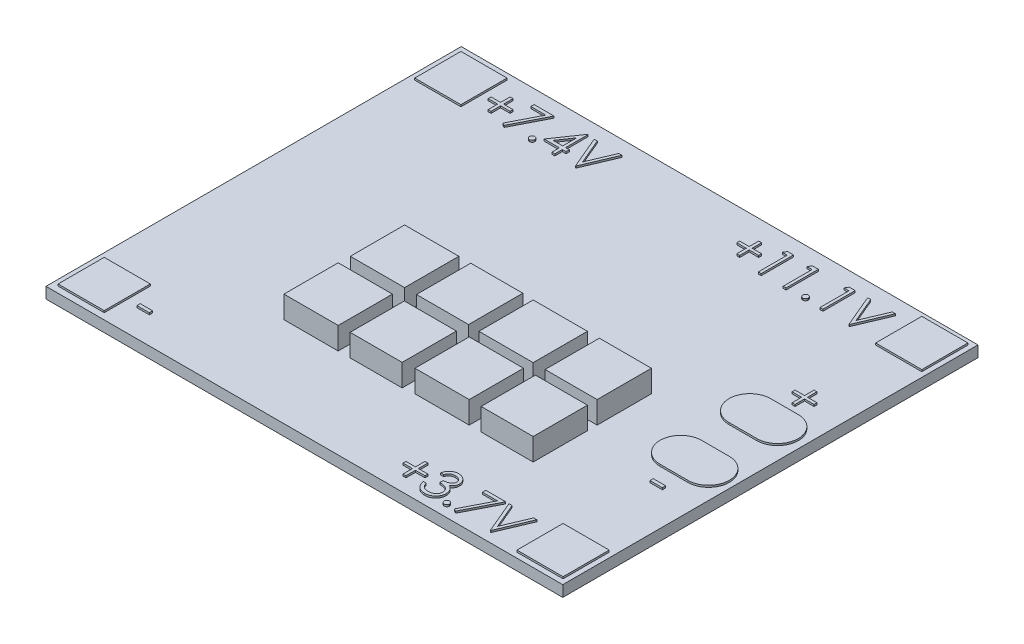
SolidWorks part; units mm, degrees
ref_plane "Front Plane" through (0, 0, 0) normal (0, 0, 1) x (1, 0, 0)
ref_plane "Top Plane" through (0, 0, 0) normal (0, 1, 0) x (1, 0, 0)
ref_plane "Right Plane" through (0, 0, 0) normal (1, 0, 0) x (0, 0, -1)
sketch "Sketch1" plane through (0, 0, 0) normal (0, 1, 0) x (1, 0, 0)
  line L1 (-32.877, 23.7821) -> (23.123, 23.7821)
  line L2 (-32.877, 23.7821) -> (-32.877, -21.2179)
  line L3 (-32.877, -21.2179) -> (23.123, -21.2179)
  line L4 (23.123, 23.7821) -> (23.123, -21.2179)
  dimension "D1" = 45
  dimension "D2" = 56
extrude "Boss-Extrude1" add sketch "Sketch1" along normal blind 1.2
sketch "Sketch2" plane through (0, 1.2, 0) normal (0, 1, 0) x (1, 0, 0)
  line L0 (17.5946, 23.2193) -> (22.5946, 23.2193)
  line L1 (-32.2431, 23.1087) -> (-27.2431, 23.1087)
  line L2 (-32.2431, 23.1087) -> (-32.2431, 18.1087)
  line L3 (-32.2431, 18.1087) -> (-27.2431, 18.1087)
  line L4 (-27.2431, 23.1087) -> (-27.2431, 18.1087)
  line L5 (17.5946, 23.2193) -> (17.5946, 18.2193)
  line L6 (17.5946, 18.2193) -> (22.5946, 18.2193)
  line L7 (22.5946, 23.2193) -> (22.5946, 18.2193)
  line L9 (-43.8468, 1.2821) -> (26.6265, 1.2821)
  line L10 (23.123, 23.7821) -> (-32.877, 23.7821) construction
  line L12 (22.5946, -20.655) -> (22.5946, -15.655)
  line L13 (17.5946, -15.655) -> (22.5946, -15.655)
  line L14 (17.5946, -20.655) -> (17.5946, -15.655)
  line L15 (-27.2431, -20.5444) -> (-27.2431, -15.5444)
  line L16 (-32.2431, -15.5444) -> (-27.2431, -15.5444)
  line L17 (-32.2431, -20.5444) -> (-32.2431, -15.5444)
  line L18 (-32.2431, -20.5444) -> (-27.2431, -20.5444)
  line L19 (17.5946, -20.655) -> (22.5946, -20.655)
  dimension "D1" = 5
  dimension "D2" = 5
  dimension "D3" = 5
  dimension "D4" = 5
  dimension "D5" = 22.5
extrude "Boss-Extrude2" add sketch "Sketch2" along normal blind 0.2 contours L4 L1 L2 L3 | L7 L0 L5 L6 | L14 L19 L12 L13 | L17 L18 L15 L16
sketch "Sketch3" plane through (0, 1.2, 0) normal (0, 1, 0) x (1, 0, 0)
  line L0 (17.1174, 5.0572) -> (20.1292, 5.0572) construction
  line L1 (17.1174, 7.3041) -> (20.1292, 7.3041)
  line L2 (17.1174, 2.8104) -> (20.1292, 2.8104)
  line L3 (17.2974, -2.5988) -> (20.3092, -2.5988) construction
  line L4 (17.2974, -0.3519) -> (20.3092, -0.3519)
  line L5 (17.2974, -4.8456) -> (20.3092, -4.8456)
  line L6 (-40.5161, 1.2821) -> (33.7738, 1.2821)
  line L7 (-32.877, -21.2179) -> (23.123, -21.2179) construction
  arc A0 (17.1174, 7.3041) -> (17.1174, 2.8104) centre (17.1174, 5.0572) ccw
  arc A1 (20.1292, 2.8104) -> (20.1292, 7.3041) centre (20.1292, 5.0572) ccw
  arc A2 (17.2974, -0.3519) -> (17.2974, -4.8456) centre (17.2974, -2.5988) ccw
  arc A3 (20.3092, -4.8456) -> (20.3092, -0.3519) centre (20.3092, -2.5988) ccw
  point P2 (18.6233, 5.0572)
  point P9 (18.8033, -2.5988)
  point P18 (0, 0)
  dimension "D1" = 22.5
extrude "Boss-Extrude3" add sketch "Sketch3" along normal blind 0.2 contours L5 A3 L4 A2 | L2 A1 L1 A0
sketch "Sketch4" plane through (0, 1.2, 0) normal (0, 1, 0) x (1, 0, 0)
  line L0 (-16.8523, -5.5779) -> (-10.9722, -5.5779)
  line L1 (-16.8045, 1.569) -> (-10.9244, 1.569)
  line L2 (-16.8045, 1.569) -> (-16.8045, -4.3111)
  line L3 (-16.8045, -4.3111) -> (-10.9244, -4.3111)
  line L4 (-10.9244, 1.569) -> (-10.9244, -4.3111)
  line L5 (-9.6337, 1.569) -> (-3.9926, 1.569)
  line L6 (-9.6337, 1.569) -> (-9.6337, -4.3111)
  line L7 (-9.6337, -4.3111) -> (-3.9926, -4.3111)
  line L8 (-3.9926, 1.569) -> (-3.9926, -4.3111)
  line L9 (-16.8523, -5.5779) -> (-16.8523, -11.458)
  line L10 (-16.8523, -11.458) -> (-10.9722, -11.458)
  line L11 (-10.9722, -5.5779) -> (-10.9722, -11.458)
  line L12 (-9.6815, -5.5779) -> (-4.0404, -5.5779)
  line L13 (-9.6815, -5.5779) -> (-9.6815, -11.458)
  line L14 (-9.6815, -11.458) -> (-4.0404, -11.458)
  line L15 (-4.0404, -5.5779) -> (-4.0404, -11.458)
  line L16 (-2.7975, 1.4973) -> (3.0826, 1.4973)
  line L17 (-2.7975, 1.4973) -> (-2.7975, -4.3828)
  line L18 (-2.7975, -4.3828) -> (3.0826, -4.3828)
  line L19 (3.0826, 1.4973) -> (3.0826, -4.3828)
  line L20 (4.3733, 1.4973) -> (10.0144, 1.4973)
  line L21 (4.3733, 1.4973) -> (4.3733, -4.3828)
  line L22 (4.3733, -4.3828) -> (10.0144, -4.3828)
  line L23 (10.0144, 1.4973) -> (10.0144, -4.3828)
  line L24 (-2.7975, -5.4345) -> (3.0826, -5.4345)
  line L25 (-2.7975, -5.4345) -> (-2.7975, -11.3146)
  line L26 (-2.7975, -11.3146) -> (3.0826, -11.3146)
  line L27 (3.0826, -5.4345) -> (3.0826, -11.3146)
  line L28 (4.3733, -5.4345) -> (10.0144, -5.4345)
  line L29 (4.3733, -5.4345) -> (4.3733, -11.3146)
  line L30 (4.3733, -11.3146) -> (10.0144, -11.3146)
  line L31 (10.0144, -5.4345) -> (10.0144, -11.3146)
extrude "Boss-Extrude4" add sketch "Sketch4" along normal blind 2.4
sketch "Sketch5" plane through (0, 1.2, 0) normal (0, 1, 0) x (1, 0, 0)
  text T0 "+11.1V"
  point P1 (13.8409, 18.6968)
  point P2 (4.7108, 18.6414)
  point P3 (2.1101, 18.6414)
  point P4 (0.3947, 18.5308)
extrude "Boss-Extrude5" add sketch "Sketch5" along normal blind 0.2
sketch "Sketch6" plane through (0, 1.2, 0) normal (0, 1, 0) x (1, 0, 0)
  text T0 "-"
  point P1 (-26.0788, -19.4655)
extrude "Boss-Extrude6" add sketch "Sketch6" along normal blind 0.2
sketch "Sketch7" plane through (0, 1.2, 0) normal (0, 1, 0) x (1, 0, 0)
  text T0 "+3.7V"
  point P1 (2.4133, -20.1347)
  point P2 (2.987, -20.2303)
extrude "Boss-Extrude7" add sketch "Sketch7" along normal blind 0.2
sketch "Sketch8" plane through (0, 1.2, 0) normal (0, 1, 0) x (1, 0, 0)
  text T0 "+7.4V"
  point P1 (-25.6963, 18.0619)
  point P2 (-26.6046, 18.5878)
extrude "Boss-Extrude8" add sketch "Sketch8" along normal blind 0.2
sketch "Sketch9" plane through (0, 1.2, 0) normal (0, 1, 0) x (1, 0, 0)
  text T0 "+"
  point P1 (14.2691, 8.8354)
  point P2 (16.0857, 8.0705)
  point P3 (17.3765, 7.5447)
extrude "Boss-Extrude9" add sketch "Sketch9" along normal blind 0.2
sketch "Sketch10" plane through (0, 1.2, 0) normal (0, 1, 0) x (1, 0, 0)
  text T0 "-"
  point P1 (16.8506, -7.5141)
  point P2 (17.4243, -7.7531)
  point P3 (18.1413, -8.0877)
extrude "Boss-Extrude10" add sketch "Sketch10" along normal blind 0.2
